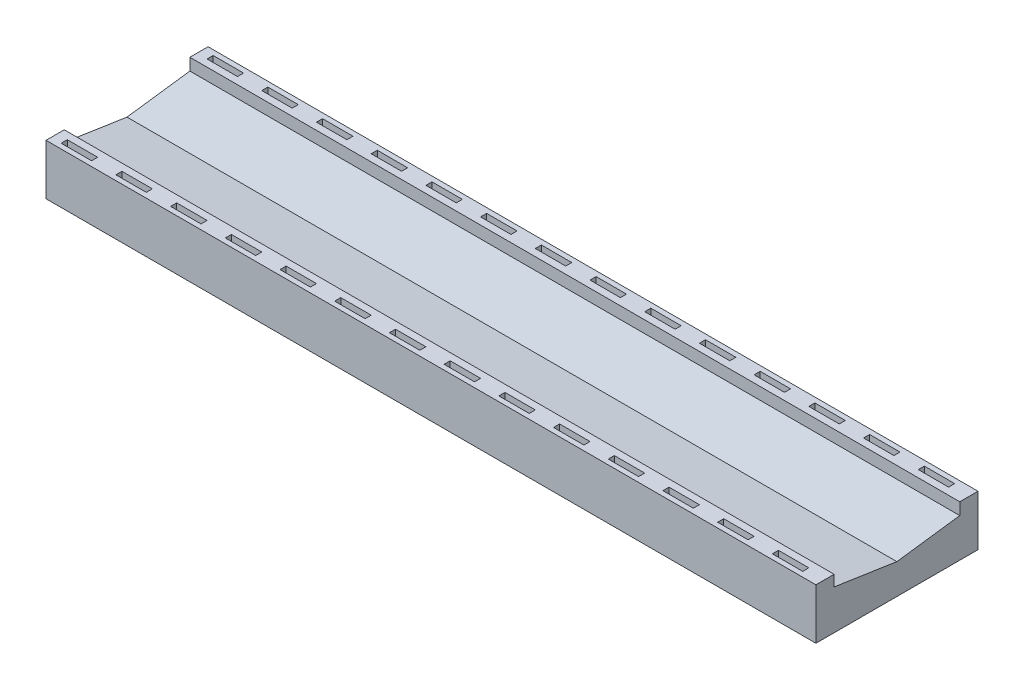
SolidWorks part; units mm, degrees
ref_plane "Front Plane" through (0, 0, 0) normal (0, 0, 1) x (1, 0, 0)
ref_plane "Top Plane" through (0, 0, 0) normal (0, 1, 0) x (1, 0, 0)
ref_plane "Right Plane" through (0, 0, 0) normal (1, 0, 0) x (0, 0, -1)
sketch "Sketch1" plane through (0, 0, 0) normal (0, 1, 0) x (1, 0, 0)
  line L1 (0, 0) -> (38, 0)
  line L2 (0, 0) -> (0, 8)
  line L3 (0, 8) -> (38, 8)
  line L4 (38, 0) -> (38, 8)
  dimension "D1" = 38
  dimension "D2" = 8
extrude "Boss-Extrude1" add sketch "Sketch1" along normal blind 2.5
sketch "Sketch2" plane through (0, 2.5, 0) normal (0, 1, 0) x (1, 0, 0)
  line L0 (0, 8) -> (0, 0) construction
  line L1 (0.5, 0.25) -> (2, 0.25)
  line L2 (0.5, 0.25) -> (0.5, 0.55)
  line L3 (0.5, 0.55) -> (2, 0.55)
  line L4 (2, 0.25) -> (2, 0.55)
  line L5 (0, 0) -> (38, 0) construction
  dimension "D1" = 0.3
  dimension "D2" = 0.5
  dimension "D3" = 1.5
  dimension "D4" = 0.25
extrude "Cut-Extrude1" cut sketch "Sketch2" against normal blind 2
pattern_linear "LPattern1" count 14 spacing 2.7 along (1, 0, 0) count 2 spacing 7.2 along (0, 0, -1) of "Cut-Extrude1"
sketch "Sketch3" plane through (0, 0, 0) normal (-1, 0, 0) x (0, 0, 1)
  line L0 (-7.1, 2.5) -> (-7.1, 1.9092)
  line L1 (-8, 2.5) -> (0, 2.5) construction
  line L2 (-7.1, 1.9092) -> (-3.9964, 1.4925)
  line L3 (-3.9964, 1.4925) -> (-0.9, 1.9596)
  line L4 (-0.9, 1.9596) -> (-0.9, 2.5)
  line L5 (0, 2.5) -> (0, 0) construction
  line L6 (-8, 2.5) -> (-8, 0) construction
  dimension "D1" = 0.9
  dimension "D2" = 0.9
extrude "Cut-Extrude3" cut sketch "Sketch3" against normal through all and the other way through all
